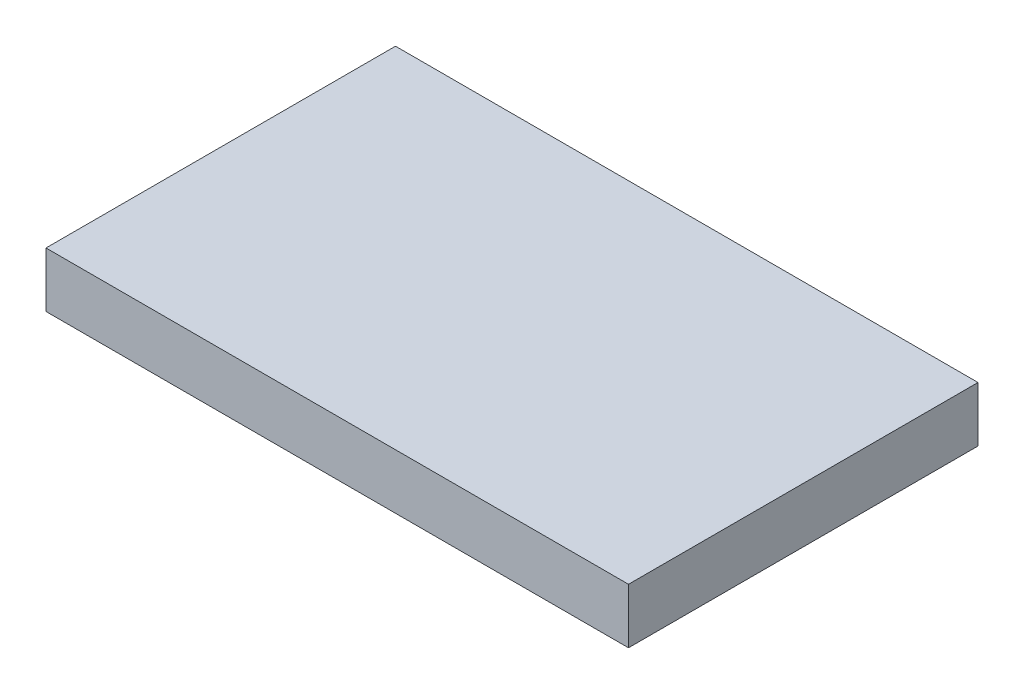
SolidWorks part; units mm, degrees
material "Melamine resin"
ref_plane "Front Plane" through (0, 0, 0) normal (0, 0, 1) x (1, 0, 0)
ref_plane "Top Plane" through (0, 0, 0) normal (0, 1, 0) x (1, 0, 0)
ref_plane "Right Plane" through (0, 0, 0) normal (1, 0, 0) x (0, 0, -1)
sketch "Sketch1" plane through (0, 0, 0) normal (0, 1, 0) x (1, 0, 0)
  line L1 (-15.875, -9.525) -> (15.875, -9.525)
  line L2 (-15.875, -9.525) -> (-15.875, 9.525)
  line L3 (-15.875, 9.525) -> (15.875, 9.525)
  line L4 (15.875, -9.525) -> (15.875, 9.525)
  line L5 (-15.875, -9.525) -> (15.875, 9.525) construction
  line L6 (-15.875, 9.525) -> (15.875, -9.525) construction
  point P0 (0, 0)
  dimension "D1" = 31.75
  dimension "D2" = 19.05
extrude "Boss-Extrude1" add sketch "Sketch1" along normal blind 3
